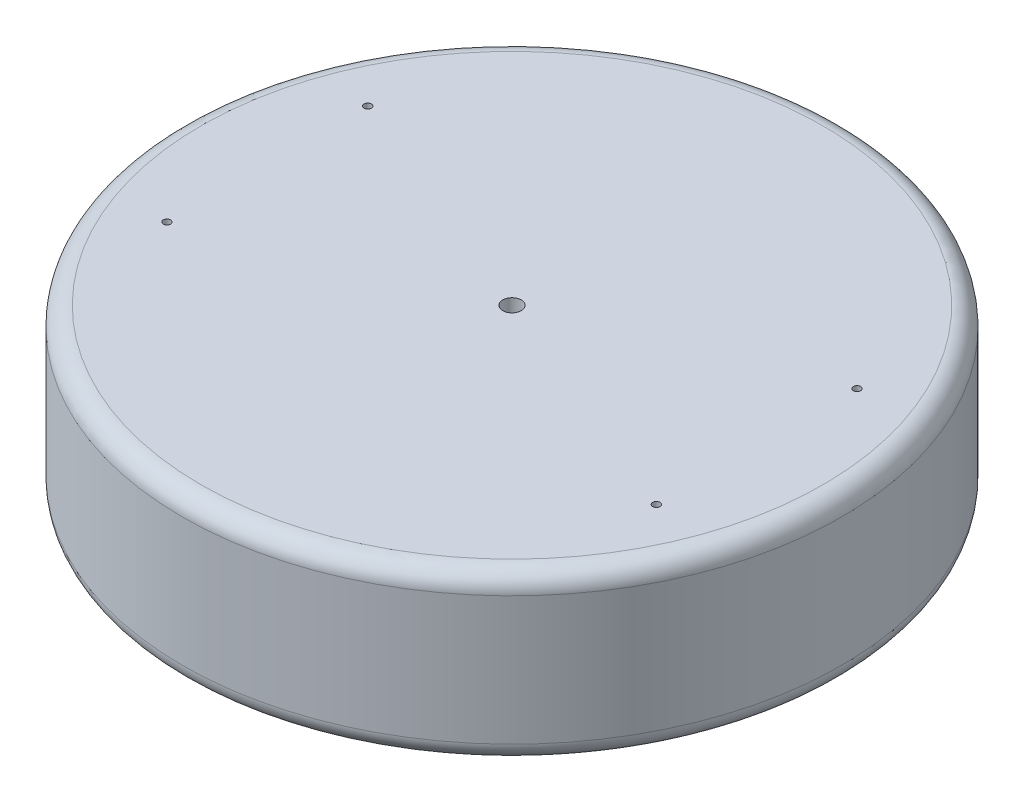
SolidWorks part; units mm, degrees
ref_plane "Front Plane" through (0, 0, 0) normal (0, 0, 1) x (1, 0, 0)
ref_plane "Top Plane" through (0, 0, 0) normal (0, 1, 0) x (1, 0, 0)
ref_plane "Right Plane" through (0, 0, 0) normal (1, 0, 0) x (0, 0, -1)
sketch "Sketch1" plane through (0, 0, 0) normal (0, 1, 0) x (1, 0, 0)
  circle A0 centre (0, 0) radius 177
  circle A1 centre (0, 0) radius 5
  dimension "D1" = 354
  dimension "D2" = 10
extrude "Boss-Extrude1" add sketch "Sketch1" along normal blind 89
sketch "Sketch2" plane through (0, 89, 0) normal (0, 1, 0) x (1, 0, 0)
  line L0 (-131.4, 53.9) -> (-131.4, -53.9) construction
  line L1 (0, 177) -> (0, 0) construction
  circle A0 centre (-131.4, 53.9) radius 1.975
  circle A1 centre (-131.4, -53.9) radius 1.975
  circle A2 centre (0, 0) radius 177 construction
  circle A3 centre (131.4, -53.9) radius 1.975
  circle A4 centre (131.4, 53.9) radius 1.975
  point P4 (-131.4, 0)
  dimension "D1" = 3.95
  dimension "D3" = 3.95
  dimension "D2" = 131.4
  dimension "D4" = 107.8
extrude "Cut-Extrude1" cut sketch "Sketch2" against normal blind 19
fillet "Fillet1" radius 10 2 edges at (0, 0, 177) (0, 89, 177)
